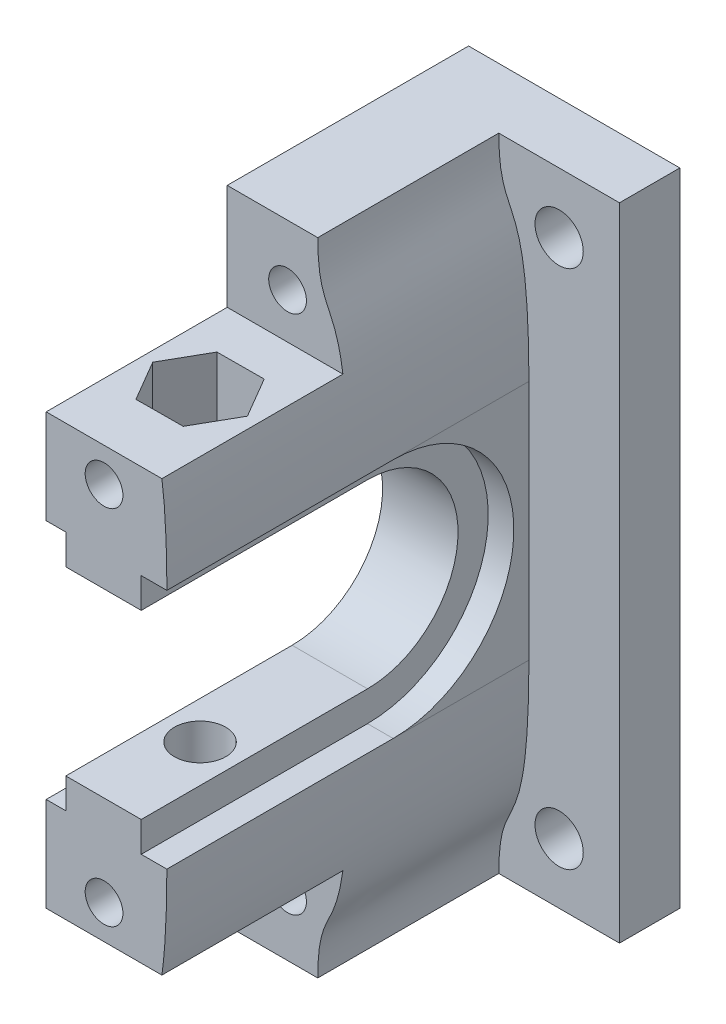
SolidWorks part; units mm, degrees
material "Acier non allié"
ref_plane "Plan de face" through (0, 0, 0) normal (0, 0, 1) x (1, 0, 0)
ref_plane "Plan de dessus" through (0, 0, 0) normal (0, 1, 0) x (1, 0, 0)
ref_plane "Plan de droite" through (0, 0, 0) normal (1, 0, 0) x (0, 0, -1)
sketch "Esquisse1" plane through (0, 0, 0) normal (0, 0, 1) x (1, 0, 0)
  line L0 (-1.3845, 0) -> (38.6155, 0) construction
  line L1 (38.6155, 42.5) -> (24.6155, 42.5)
  line L2 (38.6155, 42.5) -> (38.6155, 0)
  line L3 (38.6155, 0) -> (24.6155, 0)
  line L4 (24.6155, 42.5) -> (24.6155, 0)
  circle A0 centre (34.6155, 4) radius 1.6 construction
  circle A1 centre (34.6155, 4) radius 1.6
  circle A2 centre (34.6155, 38.5) radius 1.6 construction
  circle A3 centre (34.6155, 38.5) radius 1.6
  point P15 (38.6155, 31.9517)
  dimension "D1" = 14
  dimension "D2" = 4
extrude "Boss.-Extru.1" add sketch "Esquisse1" along normal blind 4
sketch "Esquisse2" plane through (0, 0, 4) normal (0, 0, 1) x (1, 0, 0)
  line L0 (24.6155, 0) -> (38.6155, 0) construction
  line L1 (24.6155, 42.5) -> (32.6155, 42.5)
  line L2 (24.6155, 42.5) -> (24.6155, 0)
  line L3 (24.6155, 0) -> (32.6155, 0)
  line L4 (32.6155, 42.5) -> (32.6155, 0)
  dimension "D1" = 8
extrude "Boss.-Extru.2" add sketch "Esquisse2" along normal blind 24
sketch "Esquisse3" plane through (32.6155, 0, 0) normal (1, 0, 0) x (0, 0, -1)
  line L0 (-28, 21.25) -> (-4, 21.25) construction
  line L1 (-28, 0) -> (-28, 42.5) construction
  line L2 (-4, 0) -> (-4, 42.5) construction
  line L3 (-13, 27.25) -> (-28, 27.25)
  line L4 (-28, 27.25) -> (-28, 15.25)
  line L5 (-28, 15.25) -> (-13, 15.25)
  arc A0 (-13, 15.25) -> (-13, 27.25) centre (-13, 21.25) ccw
  dimension "D1" = 12
  dimension "D2" = 9
extrude "Enlèv. mat.-Extru.1" cut sketch "Esquisse3" against normal through all
sketch "Esquisse7" plane through (32.6155, 0, 0) normal (1, 0, 0) x (0, 0, -1)
  line L0 (-13, 13.25) -> (-28, 13.25)
  line L1 (-28, 0) -> (-28, 15.25) construction
  line L2 (-28, 13.25) -> (-28, 29.25)
  line L3 (-28, 27.25) -> (-28, 42.5) construction
  line L4 (-28, 29.25) -> (-13, 29.25)
  arc A0 (-13, 13.25) -> (-13, 29.25) centre (-13, 21.25) ccw
extrude "Enlèv. mat.-Extru.3" cut sketch "Esquisse7" against normal up to surface (1.7 mm away)
sketch "Esquisse8" plane through (24.6155, 0, 0) normal (-1, 0, 0) x (0, 0, 1)
  line L3 (13, 13.25) -> (28, 13.25)
  line L4 (28, 13.25) -> (28, 29.25)
  line L5 (28, 29.25) -> (13, 29.25)
  line L6 (13, 13.25) -> (28, 13.25)
  line L7 (28, 13.25) -> (28, 29.25)
  line L8 (28, 29.25) -> (13, 29.25)
  arc A1 (13, 29.25) -> (13, 13.25) centre (13, 21.25) ccw
  arc A2 (13, 29.25) -> (13, 13.25) centre (13, 21.25) ccw
  dimension "D1" = 0
extrude "Enlèv. mat.-Extru.4" cut sketch "Esquisse8" against normal up to surface (1.3 mm away)
sketch "Esquisse6" plane through (32.6155, 0, 0) normal (1, 0, 0) x (0, 0, -1)
  line L1 (-28, 42.5) -> (-16, 42.5)
  line L2 (-28, 42.5) -> (-28, 35.5)
  line L3 (-28, 35.5) -> (-16, 35.5)
  line L4 (-16, 42.5) -> (-16, 35.5)
  line L5 (-28, 0) -> (-16, 0)
  line L6 (-28, 0) -> (-28, 7)
  line L7 (-28, 7) -> (-16, 7)
  line L8 (-16, 0) -> (-16, 7)
  dimension "D1" = 12
  dimension "D2" = 7
extrude "Enlèv. mat.-Extru.2" cut sketch "Esquisse6" against normal through all
hole_wizard "Chambrage pour vis à tête hexagonale M31" positions "Esquisse11" profile "Esquisse12" counterbore size "M3" standard "Din"
sketch "Esquisse11" plane through (0, 7, 0) normal (0, -1, 0) x (-1, 0, 0)
  line L0 (-25.9155, -13) -> (-25.9155, -28) construction
  line L3 (-24.6155, -28) -> (-32.6155, -28) construction
  point P0 (-28.4155, -21.6)
  dimension "D1" = 2.5
  dimension "D2" = 6.4
sketch "Esquisse12" plane through (28.4155, 7, 21.6) normal (1, 0, 0) x (0, 0, -1)
  line L0 (0, 0) -> (0, 31.0215)
  line L1 (0, 31.0215) -> (1.7, 30)
  line L2 (1.7, 30) -> (1.7, 3.4)
  line L3 (1.7, 3.4) -> (3.25, 3.4)
  line L4 (3.25, 3.4) -> (3.25, 0)
  line L5 (3.25, 0) -> (0, 0)
  line L10 (0, 31.0215) -> (-1.7, 30) construction
  line L11 (0, -6.35) -> (0, 107.95) construction
  dimension "Diamètre du perçage" = 3.4
  dimension "Profondeur du perçage" = 30
  dimension "Diamètre du chambrage" = 6.5
  dimension "Profondeur du chambrage" = 3.4
  dimension "Angle de pointe" = 118
hole_wizard "Trou pour taraudage pour trou taraudé M31" positions "Esquisse14" profile "Esquisse13" hole size "M3" standard "Din"
sketch "Esquisse14" plane through (0, 0, 16) normal (0, 0, 1) x (1, 0, 0)
  line L0 (28.6155, 0) -> (28.6155, 42.5) construction
  line L1 (24.6155, 0) -> (32.6155, 0) construction
  line L2 (24.6155, 42.5) -> (32.6155, 42.5) construction
  point P0 (28.6155, 4)
  point P2 (28.6155, 38.5)
  dimension "D1" = 4
  dimension "D2" = 4
  dimension "D3" = 34.5
sketch "Esquisse13" plane through (28.6155, 4, 16) normal (1, 0, 0) x (0, -1, 0)
  line L0 (0, 0) -> (0, 34.5)
  line L1 (0, 34.5) -> (1.25, 34.5)
  line L2 (1.25, 34.5) -> (1.25, 0)
  line L5 (1.25, 0) -> (0, 0)
  line L10 (0, 34.5) -> (-1.25, 34.5) construction
  line L11 (0, -6.35) -> (0, 107.95) construction
  dimension "Diamètre du perçage" = 2.5
  dimension "Profondeur du perçage" = 34.5
  dimension "Angle de pointe" = 180
sketch "Esquisse15" plane through (0, 35.5, 0) normal (0, 1, 0) x (1, 0, 0)
  line L1 (25.2979, -21.6193) -> (26.8734, -24.3096)
  line L2 (26.8734, -24.3096) -> (29.9911, -24.2903)
  line L3 (29.9911, -24.2903) -> (31.5331, -21.5807)
  line L4 (31.5331, -21.5807) -> (29.9576, -18.8904)
  line L5 (29.9576, -18.8904) -> (26.8399, -18.9097)
  line L6 (26.8399, -18.9097) -> (25.2979, -21.6193)
  circle A0 centre (28.4155, -21.6) radius 2.7 construction
  dimension "D1" = 5.4
extrude "Enlèv. mat.-Extru.5" cut sketch "Esquisse15" against normal blind 4.1
sketch "Esquisse16" plane through (0, 0, 28) normal (0, 0, 1) x (1, 0, 0)
  line L0 (24.6155, 0) -> (32.6155, 0) construction
  line L1 (30.6155, 0) -> (32.6155, 0)
  line L2 (32.6155, 0) -> (32.6155, 13.25)
  line L3 (38.6155, 21.25) -> (-1.3845, 21.25) construction
  line L4 (38.6155, 0) -> (38.6155, 42.5) construction
  line L5 (30.6155, 42.5) -> (32.6155, 42.5)
  line L6 (32.6155, 42.5) -> (32.6155, 29.25)
  spline S0 degree 3 poles (32.6155, 13.25) (32.5915, 1.6876) (30.6388, 5.5204) (30.6155, 0) knots 0 0 0 0 1 1 1 1
  spline S1 degree 3 poles (32.6155, 29.25) (32.5915, 40.8124) (30.6388, 36.9796) (30.6155, 42.5) knots 0 0 0 0 1 1 1 1
  dimension "D1" = 2
extrude "Enlèv. mat.-Extru.6" cut sketch "Esquisse16" against normal up to surface (24 mm away) up to face at (36.2155, 38.5, 4)
hole_wizard "Trou pour taraudage pour trou taraudé M32" positions "Esquisse18" profile "Esquisse17" hole size "M3" standard "Din"
sketch "Esquisse18" plane through (0, 0, 28) normal (0, 0, 1) x (1, 0, 0)
  line L0 (28.4504, 35.5) -> (28.4504, 33.25) construction
  line L1 (24.6155, 35.5) -> (32.2852, 35.5) construction
  line L2 (28.4504, 33.25) -> (28.4504, 9.25) construction
  line L3 (28.4504, 9.25) -> (28.4504, 7) construction
  line L4 (24.6155, 7) -> (32.2852, 7) construction
  line L5 (28.4504, 35.5) -> (28.4504, 33.25) construction
  line L6 (28.4504, 33.25) -> (28.4504, 9.25) construction
  line L7 (28.4504, 9.25) -> (28.4504, 7) construction
  point P0 (28.4504, 33.25)
  point P2 (28.4504, 9.25)
  dimension "D1" = 24
sketch "Esquisse17" plane through (28.4504, 33.25, 28) normal (1, 0, 0) x (0, -1, 0)
  line L0 (0, 0) -> (0, 5)
  line L1 (0, 5) -> (1.25, 5)
  line L2 (1.25, 5) -> (1.25, 0)
  line L5 (1.25, 0) -> (0, 0)
  line L10 (0, 5) -> (-1.25, 5) construction
  line L11 (0, -6.35) -> (0, 107.95) construction
  dimension "Diamètre du perçage" = 2.5
  dimension "Profondeur du perçage" = 5
  dimension "Angle de pointe" = 180
